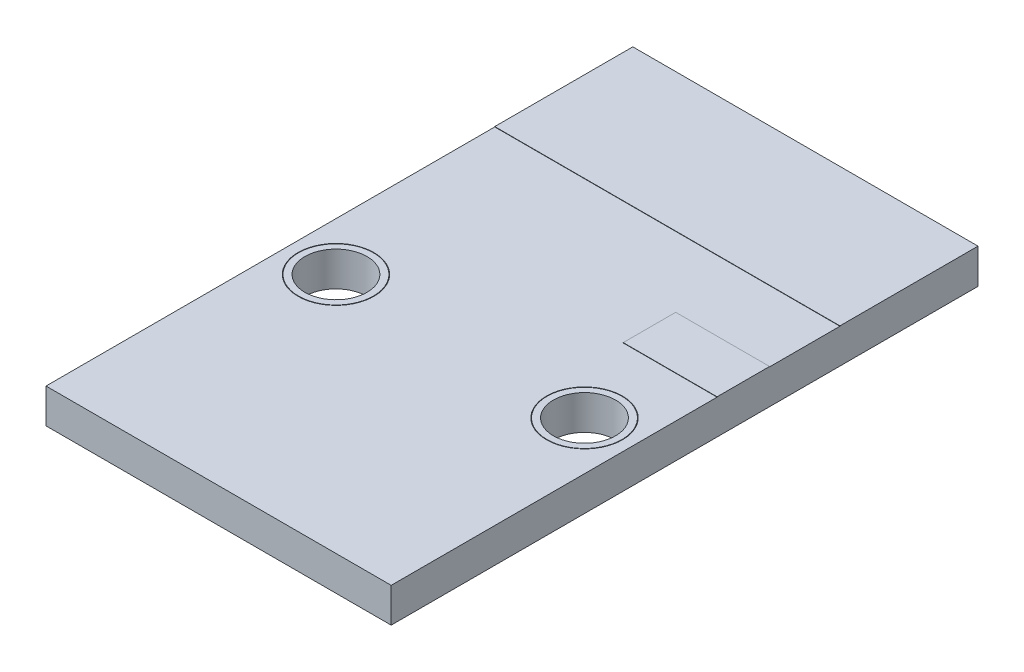
SolidWorks part; units mm, degrees
ref_plane "前视基准面" through (0, 0, 0) normal (0, 0, 1) x (1, 0, 0)
ref_plane "上视基准面" through (0, 0, 0) normal (0, 1, 0) x (1, 0, 0)
ref_plane "右视基准面" through (0, 0, 0) normal (1, 0, 0) x (0, 0, -1)
sketch "草图3" plane through (0, 0, 0) normal (0, 1, 0) x (1, 0, 0)
  line L1 (0, 0) -> (10, 0)
  line L2 (0, 0) -> (0, -17)
  line L3 (0, -17) -> (10, -17)
  line L4 (10, 0) -> (10, -17)
  dimension "D1" = 10
  dimension "D2" = 17
extrude "凸台-拉伸2" add sketch "草图3" along normal blind 1
sketch "草图4" plane through (0, 1, 0) normal (0, 1, 0) x (1, 0, 0)
  line L0 (8.6, -10) -> (10, -10) construction
  line L1 (1.4, -10) -> (0, -10) construction
  line L2 (10, -17) -> (10, 0) construction
  line L3 (0, 0) -> (0, -17) construction
  line L4 (0, -17) -> (10, -17) construction
  circle A0 centre (1.4, -10) radius 1.1
  circle A1 centre (8.6, -10) radius 1.1
  dimension "D2" = 2.2
  dimension "D1" = 1.4
  dimension "D3" = 7
extrude "切除-拉伸1" cut sketch "草图4" against normal blind 1
sketch "草图5" plane through (0, 1, 0) normal (0, 1, 0) x (1, 0, 0)
  line L0 (0, 0) -> (0, -17) construction
  line L1 (10, 0) -> (0, 0)
  line L2 (10, 0) -> (10, -4)
  line L3 (10, -4) -> (0, -4)
  line L4 (0, 0) -> (0, -4)
  dimension "D1" = 4
sketch "草图7" plane through (0, 1, 0) normal (0, 1, 0) x (1, 0, 0)
  circle A6 centre (8.6, -10) radius 1.0857
  circle A7 centre (8.6, -10) radius 0.9
  circle A8 centre (8.6, -10) radius 1.1 construction
  circle A9 centre (1.4, -10) radius 1.0854
  circle A10 centre (1.4, -10) radius 0.9
  circle A11 centre (1.4, -10) radius 1.1 construction
  dimension "D1" = 0.2
  dimension "D2" = 0.2
extrude "凸台-拉伸3" add sketch "草图7" against normal blind 1
sketch "草图8" plane through (0, 1, 0) normal (0, 1, 0) x (1, 0, 0)
  line L1 (10, 0) -> (0, 0)
  line L2 (10, 0) -> (10, -4)
  line L3 (10, -4) -> (0, -4)
  line L4 (0, 0) -> (0, -4)
extrude "凸台-拉伸4" add sketch "草图8" along normal blind 0.01
sketch "草图9" plane through (0, 1, 0) normal (0, 1, 0) x (1, 0, 0)
  line L0 (10, -17) -> (10, -4) construction
  line L1 (10, -6.0387) -> (7.2812, -6.0387)
  line L2 (10, -6.0387) -> (10, -7.5587)
  line L3 (10, -7.5587) -> (7.2812, -7.5587)
  line L4 (7.2812, -6.0387) -> (7.2812, -7.5587)
extrude "凸台-拉伸5" add sketch "草图9" along normal blind 0.01
